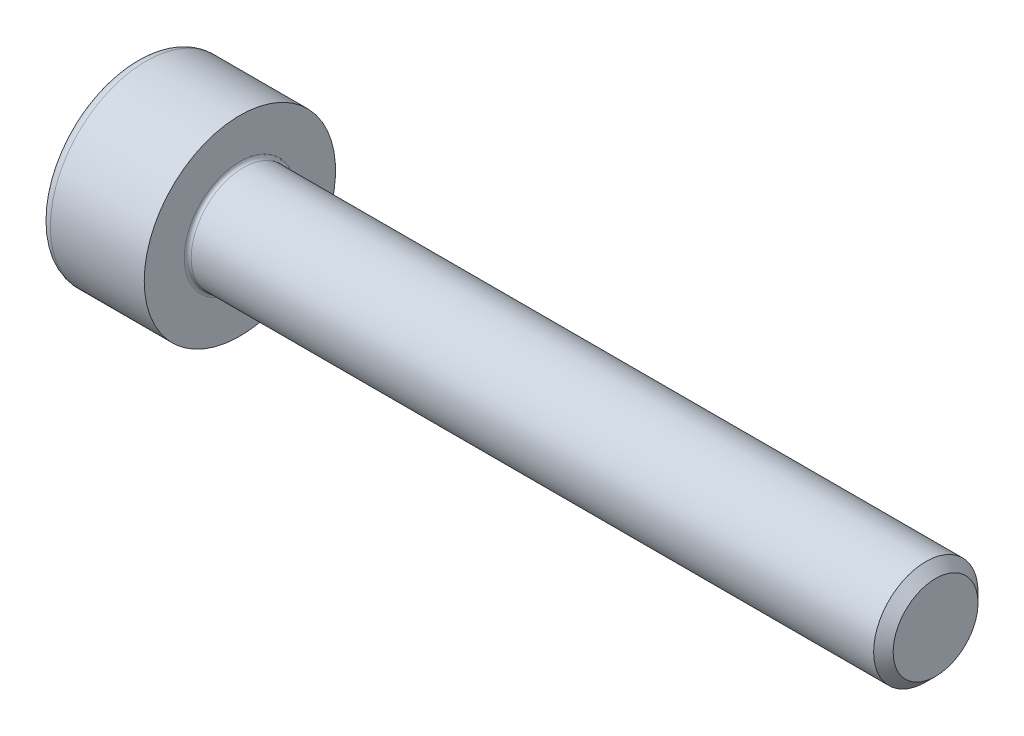
SolidWorks part; units mm, degrees
revolve "Base-Revolve" add sketch "BodySke"
sketch "BodySke" plane through (0, 0, 0) normal (0, 0, 1) x (1, 0, 0)
  line L0 (0, 0) -> (0, 2.75)
  line L1 (0, 2.75) -> (3, 2.75)
  line L2 (3, 2.75) -> (3, 1.5)
  line L3 (3, 1.5) -> (22.7195, 1.5)
  line L4 (23, 1.2195) -> (23, 0)
  line L5 (23, 0) -> (0, 0)
  line L6 (-31.75, 0) -> (127, 0) construction
  line L8 (23, 1.2195) -> (22.7195, 1.5)
  line L10 (23, -1.2195) -> (22.7195, -1.5) construction
  line L11 (3.5, 9.525) -> (3.5, 3.175) construction
  line L12 (18, 9.525) -> (18, 3.175) construction
  line L13 (-37, 9.525) -> (-37, 3.175) construction
  dimension "Head_ht" = 3
  dimension "Length" = 20
  dimension "Body_ch_ang" = 45
  dimension "Diameter" = 3
  dimension "Minor_dia" = 2.439
  dimension "Advance" = 0.5
  dimension "Thread_nom" = 5
  dimension "Thread_length" = 60
  dimension "Head_dia" = 5.5
cosmetic thread "ThreadCosmetic" [suppressed]
fillet "Fillet1" radius 0.1 1 edges at (3, 0, 1.5)
fillet "Fillet2" radius 0.3 1 edges at (0, 0, 2.75)
ref_plane "Plane1" through (0, 0, 0) normal (0, 0, 1) x (1, 0, 0)
ref_plane "Plane2" through (0, 0, 0) normal (0, 1, 0) x (1, 0, 0)
ref_plane "Plane3" through (0, 0, 0) normal (1, 0, 0) x (0, 0, -1)
other "Configuration Table"
sketch "Sketch2" plane through (0, 0, 0) normal (0, 0, 1) x (1, 0, 0)
  line L0 (0, 1.26) -> (1.3, 1.26)
  line L1 (1.3, 1.26) -> (2.0275, 0)
  line L2 (-31.75, 0) -> (127, 0) construction
  line L3 (2.0275, 0) -> (0, 0)
  line L4 (0, 0) -> (0, 1.26)
  line L6 (0, 0) -> (47.625, 0) construction
  dimension "D1" = 1.26
  dimension "D2" = 60
  dimension "Depth" = 1.3
revolve "Hex-PreBroach" cut sketch "Sketch2" angle 360 about L6
sketch "Sketch3" plane through (0, 0, 0) normal (-1, 0, 0) x (0, 0.5, 0.866)
  line L0 (0.7275, 1.26) -> (-0.7275, 1.26)
  line L1 (-0.7275, 1.26) -> (-1.4549, 0)
  line L2 (0.7275, 1.26) -> (1.4549, 0)
  line L3 (0.7275, -1.26) -> (1.4549, 0)
  line L4 (0.7275, -1.26) -> (-0.7275, -1.26)
  line L5 (-0.7275, -1.26) -> (-1.4549, 0)
  dimension "D1" = 1.26
  dimension "D2" = 1.26
  dimension "Hex_size" = 2.52
extrude "Hex" cut sketch "Sketch3" against normal blind 1.3
sketch "ThdSchSke" plane through (0, 0, 0) normal (0, 0, 1) x (1, 0, 0)
  line L0 (18, -1.2195) -> (17.8036, -1.5)
  line L1 (18, -1.2195) -> (18.1964, -1.5)
  line L2 (18.1964, -1.5) -> (18.1964, -1.875)
  line L3 (-3.175, 0) -> (5.1513, 0) construction
  line L4 (0, 2.45) -> (0, -2.45) construction
  line L5 (18.1964, -1.875) -> (17.8036, -1.875)
  line L6 (17.8036, -1.875) -> (17.8036, -1.5)
  dimension "Thread_minor" = 2.439
  dimension "Diameter" = 3
  dimension "Start" = 18
revolve "ThreadSchematic" [suppressed] cut sketch "ThdSchSke" angle 360 about L3
pattern_linear "ThdSchPat" [suppressed]
equation "\"D2@Sketch3\" = \"Hex_size@Sketch3\" / 2"
equation "\"D1@Sketch3\" = \"Hex_size@Sketch3\" / 2"
equation "\"D1@Sketch2\" = \"Hex_size@Sketch3\" / 2"
equation "\"Thread_minor@ThreadCosmetic\"  =  \"Minor_dia@BodySke\""
equation "\"Depth@Sketch2\" =  \"Key_eng@Hex\""
equation "\"Thread_length@ThreadCosmetic\" = ((sgn( (\"Length@BodySke\" - \"Advance@BodySke\" * 3.0) - \"Thread_nom@BodySke\" )-1)*( (\"Length@BodySke\" - \"Advance@BodySke\" * 3.0) - \"Thread_nom@BodySke\" ))/-2+ \"Thread_nom@BodySke\""
equation "\"Thread_minor@ThdSchSke\" = \"Minor_dia@BodySke\""
equation "\"Diameter@ThdSchSke\" = \"Diameter@BodySke\""
equation "\"Overcut@ThdSchSke\" = \"Diameter@BodySke\" * 1.25"
equation "\"Start@ThdSchSke\" = \"Head_ht@BodySke\" + \"Length@BodySke\" - \"Thread_length@ThreadCosmetic\"  '---Non-countersunk---"
equation "\"Num_threads@ThdSchPat\" = int( \"Thread_length@ThreadCosmetic\" / \"Advance@BodySke\" + 0.999 )  + 1"
equation "\"Advance@ThdSchPat\" = \"Thread_length@ThreadCosmetic\" /  (\"Num_threads@ThdSchPat\" - 1) 'relax it"
equation "\"Num_threads@ThdSchPat\" = \"Num_threads@ThdSchPat\" - sgn( \"Num_threads@ThdSchPat\" - 1) '---chamfered tips only---"
